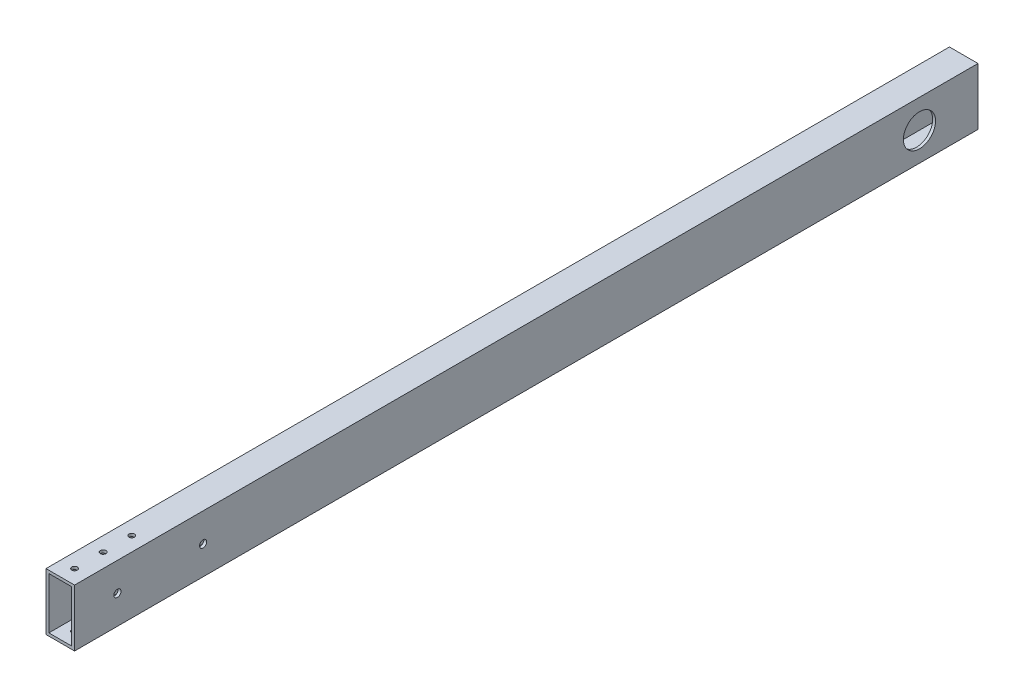
SolidWorks part; units mm, degrees
ref_plane "Front Plane" through (0, 0, 0) normal (0, 0, 1) x (1, 0, 0)
ref_plane "Top Plane" through (0, 0, 0) normal (0, 1, 0) x (1, 0, 0)
ref_plane "Right Plane" through (0, 0, 0) normal (1, 0, 0) x (0, 0, -1)
sketch "Sketch1" plane through (0, 0, 0) normal (0, 0, 1) x (1, 0, 0)
  line L1 (-12.7, -25.4) -> (12.7, -25.4)
  line L2 (-12.7, -25.4) -> (-12.7, 25.4)
  line L3 (-12.7, 25.4) -> (12.7, 25.4)
  line L4 (12.7, -25.4) -> (12.7, 25.4)
  line L5 (-12.7, -25.4) -> (12.7, 25.4) construction
  line L6 (-12.7, 25.4) -> (12.7, -25.4) construction
  point P0 (0, 0)
  dimension "D1" = 25.4
  dimension "D2" = 50.8
extrude "Extrude-Thin1" add sketch "Sketch1" along normal mid plane 803.275 thin thin type one direction reverse wall 2.54
sketch "Sketch2" plane through (-12.7, 0, 0) normal (-1, 0, 0) x (0, 0, 1)
  circle A0 centre (-349.5948, 0) radius 14.2875
  dimension "D1" = 28.575
extrude "Cut-Extrude1" cut sketch "Sketch2" against normal through all
sketch "Sketch3" plane through (-12.7, 0, 0) normal (-1, 0, 0) x (0, 0, 1)
  line L0 (401.6375, 25.4) -> (401.6375, -25.4) construction
  circle A0 centre (363.5375, 0) radius 3.175
  circle A1 centre (287.3375, 0) radius 3.175
  dimension "D1" = 6.35
  dimension "D2" = 6.35
  dimension "D3" = 38.1
  dimension "D4" = 76.2
extrude "Cut-Extrude2" cut sketch "Sketch3" against normal through all
sketch "Sketch5" plane through (0, -25.4, 0) normal (0, -1, 0) x (1, 0, 0)
  circle A0 centre (0, 228.8658) radius 2.4765
  circle A1 centre (0, 152.6658) radius 2.4765
extrude "Cut-Extrude4" cut sketch "Sketch5" against normal blind 3.81
sketch "Sketch7" plane through (0, 25.4, 0) normal (0, 1, 0) x (1, 0, 0)
  circle A0 centre (0, -338.1375) radius 2.4765
  circle A1 centre (0, -363.5375) radius 2.4765
  circle A2 centre (0, -388.9375) radius 2.4765
extrude "Cut-Extrude5" cut sketch "Sketch7" against normal through all
sketch "Sketch8" plane through (0, -25.4, 0) normal (0, -1, 0) x (1, 0, 0)
  circle A0 centre (-5.0013, -196.8119) radius 2.4765
  circle A1 centre (-5.0483, -184.112) radius 2.4765
extrude "Cut-Extrude6" cut sketch "Sketch8" against normal blind 3.81
sketch "Sketch9" [suppressed] plane through (0, -25.4, 0) normal (0, -1, 0) x (1, 0, 0)
  circle A0 centre (5.0013, -196.8119) radius 2.4892
  circle A1 centre (5.0013, -184.1119) radius 2.4892
extrude "Cut-Extrude7" [suppressed] cut sketch "Sketch9" against normal blind 3.81
